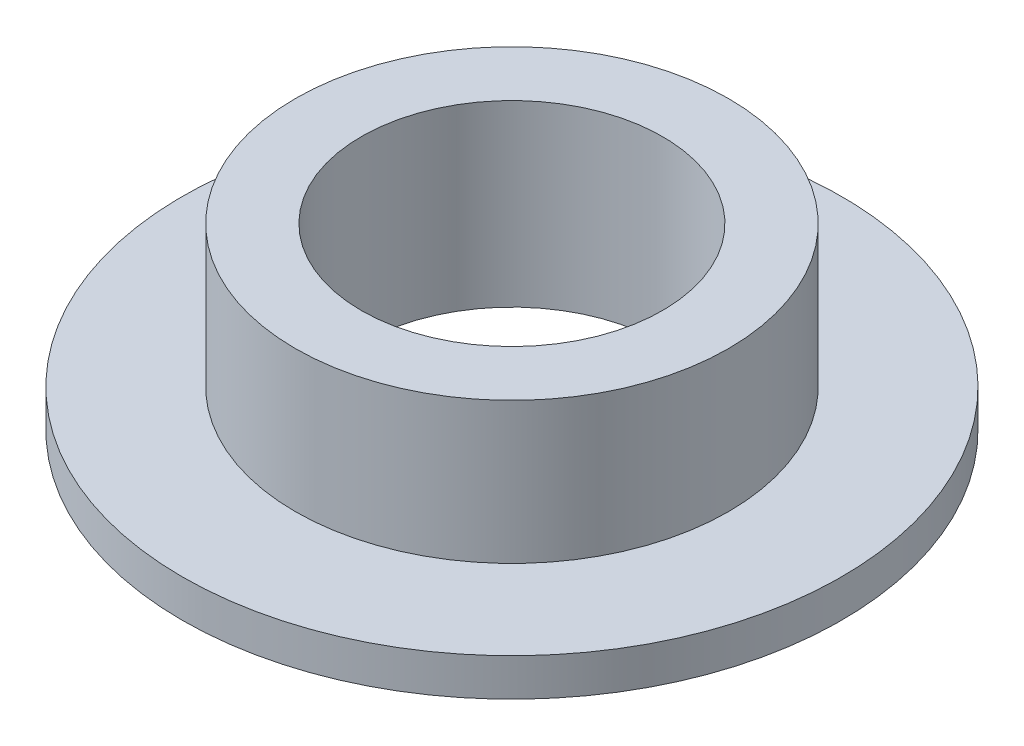
SolidWorks part; units mm, degrees
ref_plane "Front Plane" through (0, 0, 0) normal (0, 0, 1) x (1, 0, 0)
ref_plane "Top Plane" through (0, 0, 0) normal (0, 1, 0) x (1, 0, 0)
ref_plane "Right Plane" through (0, 0, 0) normal (1, 0, 0) x (0, 0, -1)
sketch "Sketch1" plane through (0, 0, 0) normal (0, 1, 0) x (1, 0, 0)
  circle A0 centre (0, 0) radius 3.5
  dimension "D1" = 7
extrude "Boss-Extrude1" add sketch "Sketch1" along normal blind 0.4
sketch "Sketch2" plane through (0, 0.4, 0) normal (0, 1, 0) x (1, 0, 0)
  circle A0 centre (0, 0) radius 2.3
  dimension "D1" = 4.6
extrude "Boss-Extrude2" add sketch "Sketch2" along normal blind 1.5
sketch "Sketch3" plane through (0, 1.9, 0) normal (0, 1, 0) x (1, 0, 0)
  circle A0 centre (0, 0) radius 1.6
  dimension "D1" = 3.2
extrude "Cut-Extrude1" cut sketch "Sketch3" against normal blind 16
